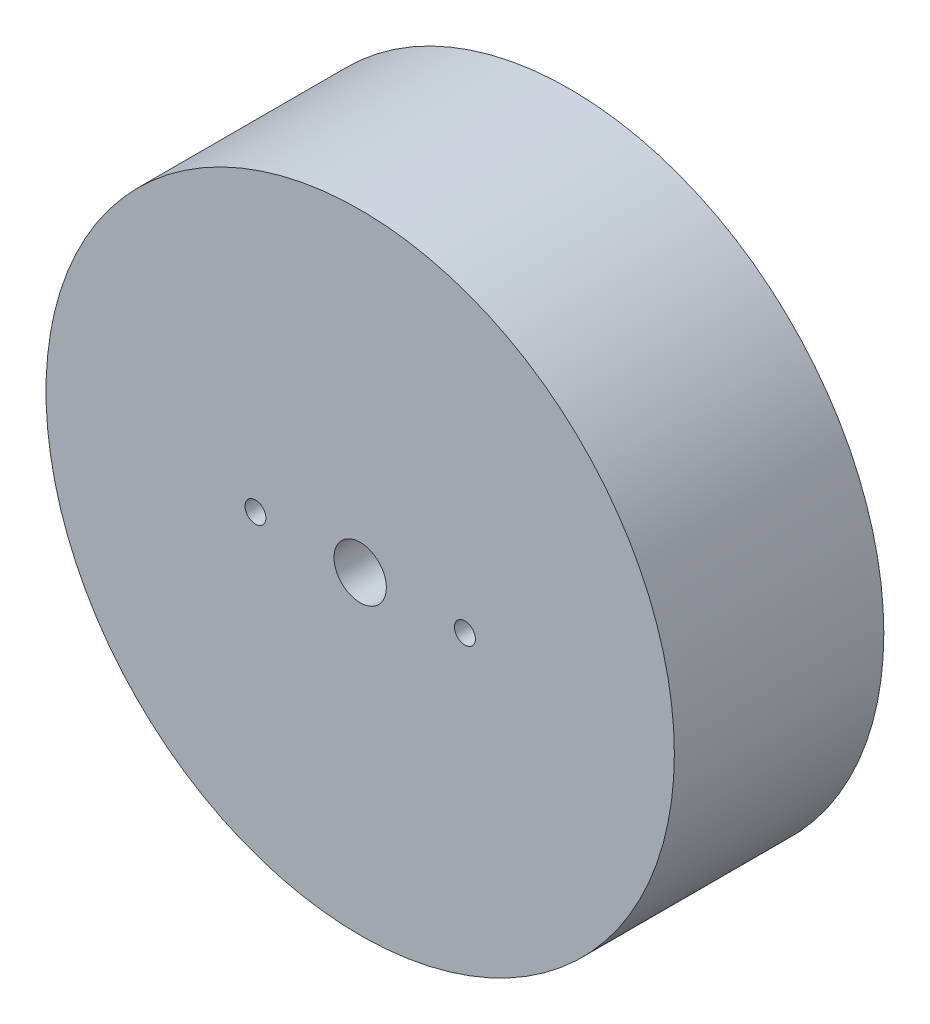
SolidWorks part; units mm, degrees
ref_plane "Front Plane" through (0, 0, 0) normal (0, 0, 1) x (1, 0, 0)
ref_plane "Top Plane" through (0, 0, 0) normal (0, 1, 0) x (1, 0, 0)
ref_plane "Right Plane" through (0, 0, 0) normal (1, 0, 0) x (0, 0, -1)
sketch "Sketch1" plane through (0, 0, 0) normal (0, 0, 1) x (1, 0, 0)
  circle A0 centre (0, 0) radius 30
  circle A1 centre (10, 0) radius 1
  circle A2 centre (-10, 0) radius 1
extrude "Boss-Extrude1" add sketch "Sketch1" along normal blind 20
sketch "Sketch3" plane through (0, 0, 20) normal (0, 0, 1) x (1, 0, 0)
  circle A0 centre (0, 0) radius 2.5
extrude "Cut-Extrude1" cut sketch "Sketch3" against normal through all
